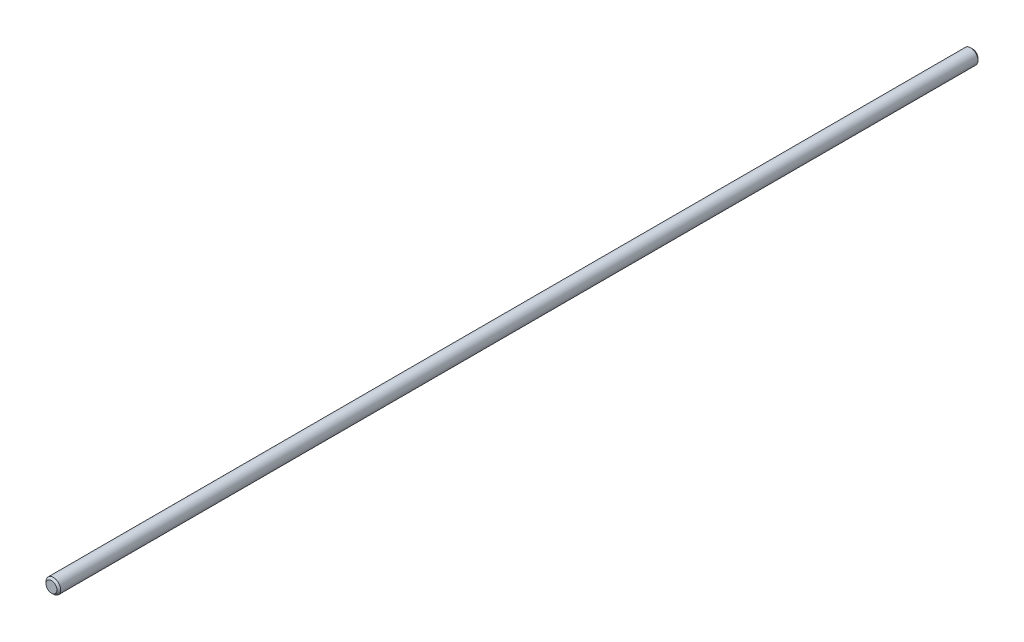
SolidWorks part; units mm, degrees
ref_plane "Front Plane" through (0, 0, 0) normal (0, 0, 1) x (1, 0, 0)
ref_plane "Top Plane" through (0, 0, 0) normal (0, 1, 0) x (1, 0, 0)
ref_plane "Right Plane" through (0, 0, 0) normal (1, 0, 0) x (0, 0, -1)
sketch "Sketch1" plane through (0, 0, 0) normal (0, 0, 1) x (1, 0, 0)
  circle A0 centre (0, 0) radius 3.975
  dimension "D1" = 7.95
extrude "Boss-Extrude1" add sketch "Sketch1" along normal blind 500
chamfer "Chamfer1" distance 1 angle 45 2 edges at (3.975, 0, 0) (3.975, 0, 500)
